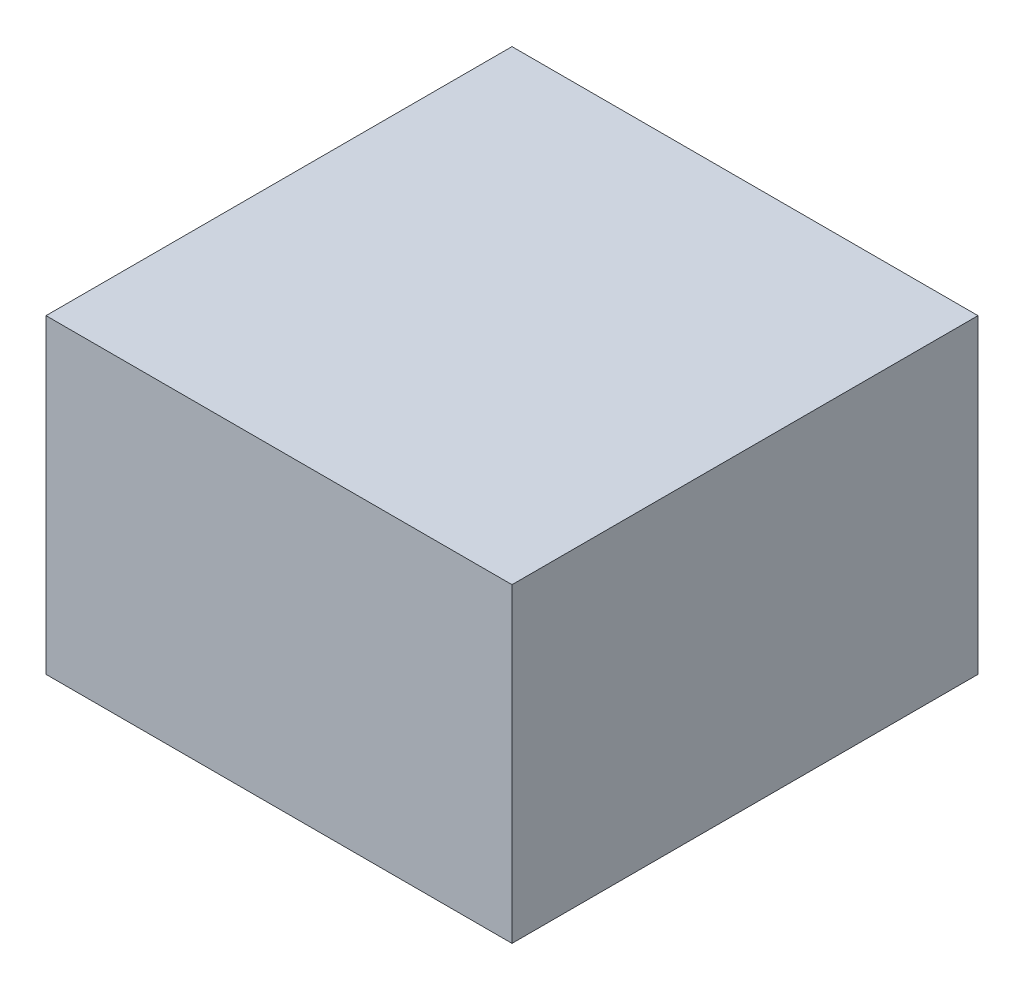
SolidWorks part; units mm, degrees
ref_plane "Front Plane" through (0, 0, 0) normal (0, 0, 1) x (1, 0, 0)
ref_plane "Top Plane" through (0, 0, 0) normal (0, 1, 0) x (1, 0, 0)
ref_plane "Right Plane" through (0, 0, 0) normal (1, 0, 0) x (0, 0, -1)
sketch "Sketch1" plane through (0, 0, 0) normal (0, 1, 0) x (1, 0, 0)
  line L1 (0, 0) -> (-150, 0)
  line L2 (0, 0) -> (0, 150)
  line L3 (0, 150) -> (-150, 150)
  line L4 (-150, 0) -> (-150, 150)
  dimension "D1" = 150
  dimension "D2" = 150
extrude "Extrude1" add sketch "Sketch1" along normal blind 100
